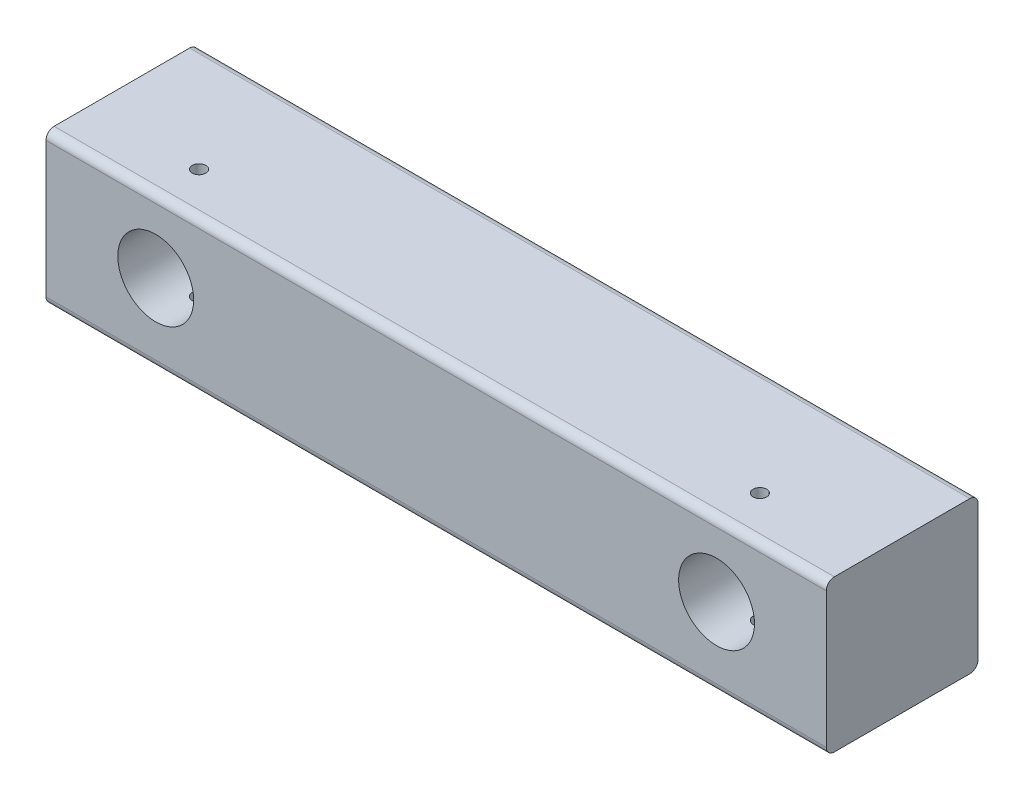
SolidWorks part; units mm, degrees
material "Pine"
ref_plane "Front Plane" through (0, 0, 0) normal (0, 0, 1) x (1, 0, 0)
ref_plane "Top Plane" through (0, 0, 0) normal (0, 1, 0) x (1, 0, 0)
ref_plane "Right Plane" through (0, 0, 0) normal (1, 0, 0) x (0, 0, -1)
sketch "Sketch1" plane through (0, 0, 0) normal (0, 0, 1) x (1, 0, 0)
  line L1 (-228.6, -571.9939) -> (228.6, -571.9939)
  line L2 (-228.6, -571.9939) -> (-228.6, -483.0939)
  line L3 (-228.6, -483.0939) -> (228.6, -483.0939)
  line L4 (228.6, -571.9939) -> (228.6, -483.0939)
extrude "Boss-Extrude1" add sketch "Sketch1" against normal up to surface (88.9 mm away)
sketch "Sketch2" plane through (0, 0, 0) normal (0, 0, 1) x (1, 0, 0)
  circle A0 centre (164.3095, -525.6072) radius 22.225 construction
  circle A1 centre (-164.3095, -525.6072) radius 22.225 construction
  circle A2 centre (164.3095, -525.6072) radius 22.225
  circle A3 centre (-164.3095, -525.6072) radius 22.225
extrude "Cut-Extrude1" cut sketch "Sketch2" against normal through all
hole_wizard "5/16 (0.3125) Diameter Hole1" positions "Sketch3" profile "Sketch4" hole size "5/16" standard "ANSI Inch" end condition through all
sketch "Sketch3" plane through (0, -483.0939, 0) normal (0, 1, 0) x (1, 0, 0)
  circle A0 centre (164.3095, 25.4) radius 3.9687 construction
  circle A1 centre (-164.3095, 25.4) radius 3.9687 construction
  point P0 (-164.3095, 25.4)
  point P2 (164.3095, 25.4)
sketch "Sketch4" plane through (-164.3095, -483.0939, -25.4) normal (1, 0, 0) x (0, 0, 1)
  line L0 (0, 0) -> (0, 88.9)
  line L1 (0, 88.9) -> (3.9687, 88.9)
  line L2 (3.9687, 88.9) -> (3.9687, 0)
  line L5 (3.9687, 0) -> (0, 0)
  line L11 (0, -6.35) -> (0, 107.95) construction
  dimension "Thru Hole Dia." = 7.9375
  dimension "Thru Hole Depth" = 88.9
fillet "Fillet1" radius 4.7625 4 edges at (0, -571.9939, 0) (0, -483.0939, -88.9) (0, -571.9939, -88.9) (0, -483.0939, 0)
